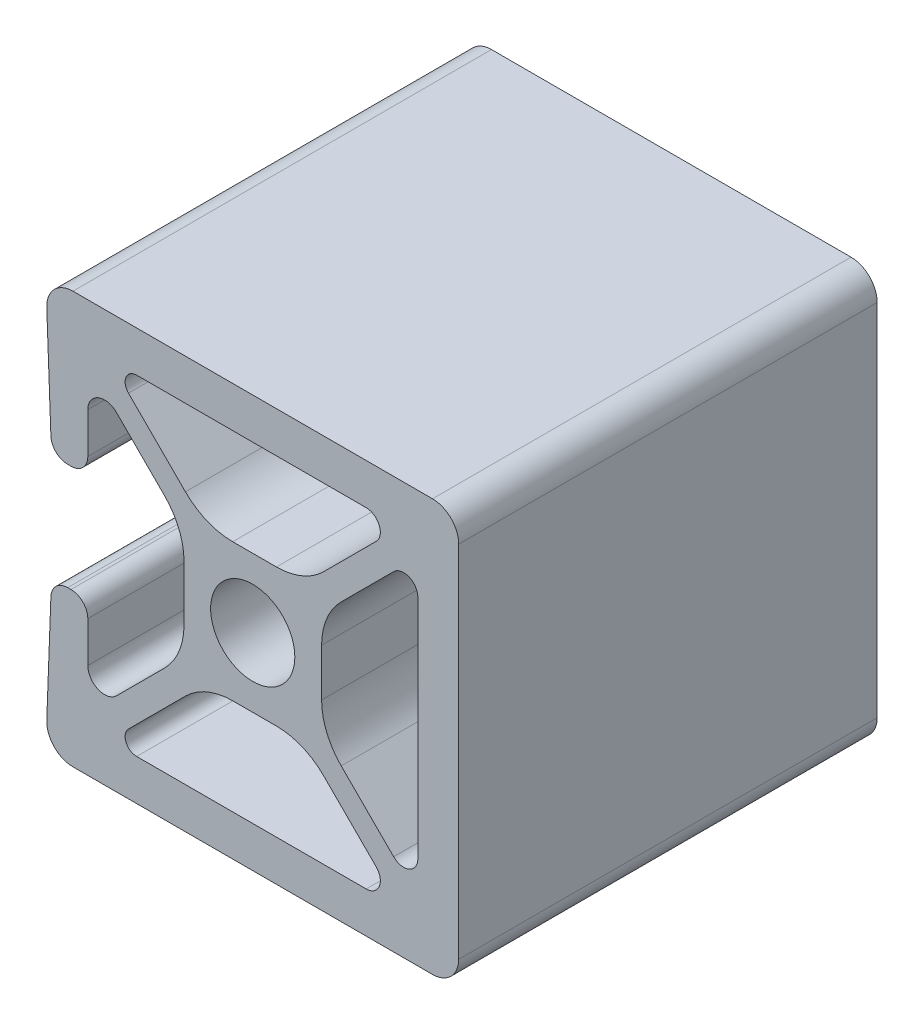
SolidWorks part; units mm, degrees
material "6061 Alloy"
ref_plane "Front" through (0, 0, 0) normal (0, 0, 1) x (1, 0, 0)
ref_plane "Top" through (0, 0, 0) normal (0, 1, 0) x (1, 0, 0)
ref_plane "Right" through (0, 0, 0) normal (1, 0, 0) x (0, 0, -1)
sketch "Sketch1" plane through (0, 0, 0) normal (0, 0, 1) x (1, 0, 0)
  line L0 (-7.54, 8.825) -> (-4.0841, 5.3691)
  line L1 (0, 10.02) -> (-7.045, 10.02)
  line L2 (0, 10.02) -> (6.885, 10.02)
  line L3 (0, 4.18) -> (-1.2132, 4.18)
  line L4 (0, 4.18) -> (1.4395, 4.18)
  line L5 (7.4931, 8.5519) -> (4.3104, 5.3691)
  line L6 (-8.268, 7.4462) -> (-5.3584, 4.5366)
  line L7 (-10.0093, 4.26) -> (-10.0093, 6.725)
  line L8 (-4.1693, 0) -> (-4.1693, 1.6658)
  line L9 (-11.23, 3.24) -> (-11.0293, 3.24)
  line L10 (-4.1693, 0) -> (-4.1693, -1.6658)
  line L11 (-12.2493, 4.2216) -> (-12.4989, 10.8502)
  line L12 (-8.268, -7.4462) -> (-5.3584, -4.5366)
  line L13 (0, 12.5) -> (-10.91, 12.5)
  line L14 (-10.0093, -4.26) -> (-10.0093, -6.725)
  line L15 (0, 12.5) -> (10.91, 12.5)
  line L16 (-11.23, -3.24) -> (-11.0293, -3.24)
  line L17 (12.5, -10.91) -> (12.5, 10.91)
  line L18 (-12.2493, -4.2216) -> (-12.4989, -10.8502)
  line L19 (0, -12.5) -> (10.91, -12.5)
  line L20 (0, -12.5) -> (-10.91, -12.5)
  line L21 (0, -10.02) -> (-7.045, -10.02)
  line L22 (-7.54, -8.825) -> (-4.0841, -5.3691)
  line L23 (0, -10.02) -> (6.885, -10.02)
  line L24 (0, -4.18) -> (-1.2132, -4.18)
  line L25 (7.4931, -8.5519) -> (4.3104, -5.3691)
  line L26 (0, -4.18) -> (1.4395, -4.18)
  line L27 (8.5519, 7.4931) -> (5.3691, 4.3104)
  line L28 (10.02, -6.885) -> (10.02, 6.885)
  line L29 (4.18, -1.4395) -> (4.18, 1.4395)
  line L30 (8.5519, -7.4931) -> (5.3691, -4.3104)
  arc A0 (-7.045, 10.02) -> (-7.54, 8.825) centre (-7.045, 9.32) ccw
  arc A1 (-4.0841, 5.3691) -> (-1.2132, 4.18) centre (-1.2132, 8.24) ccw
  arc A2 (7.4931, 8.5519) -> (6.885, 10.02) centre (6.885, 9.16) ccw
  arc A3 (1.4395, 4.18) -> (4.3104, 5.3691) centre (1.4395, 8.24) ccw
  arc A4 (-8.268, 7.4462) -> (-10.0093, 6.725) centre (-8.9893, 6.725) ccw
  arc A5 (-4.1693, 1.6658) -> (-5.3584, 4.5366) centre (-8.2293, 1.6658) ccw
  arc A6 (-11.0293, 3.24) -> (-10.0093, 4.26) centre (-11.0293, 4.26) ccw
  arc A7 (-12.2493, 4.2216) -> (-11.23, 3.24) centre (-11.23, 4.26) ccw
  arc A8 (-5.3584, -4.5366) -> (-4.1693, -1.6658) centre (-8.2293, -1.6658) ccw
  arc A9 (-10.91, 12.5) -> (-12.4989, 10.8502) centre (-10.91, 10.91) ccw
  arc A10 (-10.0093, -6.725) -> (-8.268, -7.4462) centre (-8.9893, -6.725) ccw
  arc A11 (-10.0093, -4.26) -> (-11.0293, -3.24) centre (-11.0293, -4.26) ccw
  arc A12 (12.5, 10.91) -> (10.91, 12.5) centre (10.91, 10.91) ccw
  arc A13 (-11.23, -3.24) -> (-12.2493, -4.2216) centre (-11.23, -4.26) ccw
  arc A14 (10.91, -12.5) -> (12.5, -10.91) centre (10.91, -10.91) ccw
  arc A15 (-12.4989, -10.8502) -> (-10.91, -12.5) centre (-10.91, -10.91) ccw
  arc A16 (-7.54, -8.825) -> (-7.045, -10.02) centre (-7.045, -9.32) ccw
  arc A17 (-1.2132, -4.18) -> (-4.0841, -5.3691) centre (-1.2132, -8.24) ccw
  arc A18 (6.885, -10.02) -> (7.4931, -8.5519) centre (6.885, -9.16) ccw
  arc A19 (4.3104, -5.3691) -> (1.4395, -4.18) centre (1.4395, -8.24) ccw
  arc A20 (0, 2.555) -> (-2.555, 0) centre (0, 0) ccw
  arc A21 (-2.555, 0) -> (0, -2.555) centre (0, 0) ccw
  arc A22 (2.555, 0) -> (0, 2.555) centre (0, 0) ccw
  arc A23 (0, -2.555) -> (2.555, 0) centre (0, 0) ccw
  arc A24 (10.02, 6.885) -> (8.5519, 7.4931) centre (9.16, 6.885) ccw
  arc A25 (5.3691, 4.3104) -> (4.18, 1.4395) centre (8.24, 1.4395) ccw
  arc A26 (8.5519, -7.4931) -> (10.02, -6.885) centre (9.16, -6.885) ccw
  arc A27 (4.18, -1.4395) -> (5.3691, -4.3104) centre (8.24, -1.4395) ccw
extrude "Extrude1" add sketch "Sketch1" along normal blind 25.4
